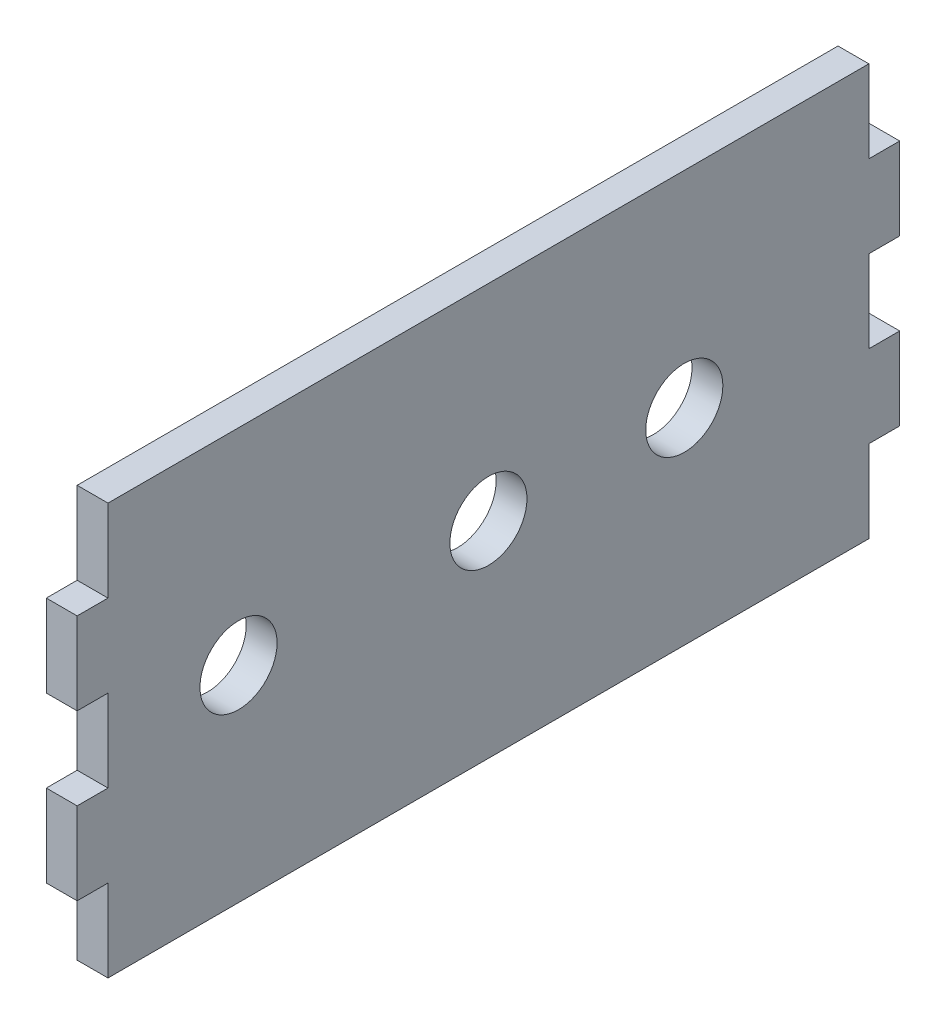
SolidWorks part; units mm, degrees
ref_plane "Alzado" through (0, 0, 0) normal (0, 0, 1) x (1, 0, 0)
ref_plane "Planta" through (0, 0, 0) normal (0, 1, 0) x (1, 0, 0)
ref_plane "Vista lateral" through (0, 0, 0) normal (1, 0, 0) x (0, 0, -1)
sketch "Croquis1" plane through (0, 0, 0) normal (1, 0, 0) x (0, 0, -1)
  line L0 (0, 40) -> (0, -40) construction
  line L1 (80, -40) -> (-80, -40)
  line L2 (80, -40) -> (80, 40)
  line L3 (80, 40) -> (-80, 40)
  line L4 (-80, -40) -> (-80, 40)
  line L5 (80, -40) -> (-80, 40) construction
  line L6 (80, 40) -> (-80, -40) construction
  point P0 (0, 0)
  dimension "D1" = 160
  dimension "D2" = 80
extrude "Saliente-Extruir1" add sketch "Croquis1" along normal blind 6
sketch "Croquis2" plane through (6, 0, 0) normal (1, 0, 0) x (0, 0, -1)
  line L1 (-80, -40) -> (80, -40) construction
  line L2 (-80, 40) -> (-80, -40) construction
  circle A0 centre (-48.61, 0) radius 7.5
  circle A1 centre (0, 0) radius 7.5
  circle A2 centre (38.1, 0) radius 7.5
  dimension "D1" = 15
  dimension "D2" = 80
  dimension "D3" = 40
  dimension "D4" = 40
  dimension "D5" = 40
  dimension "D6" = 48.61
  dimension "D7" = 38.1
extrude "Cortar-Extruir1" cut sketch "Croquis2" against normal blind 6
sketch "Croquis3" plane through (6, 0, 0) normal (1, 0, 0) x (0, 0, -1)
  line L0 (0, 40) -> (0, -40) construction
  line L1 (80, 40) -> (-80, 40) construction
  line L2 (-80, -40) -> (80, -40) construction
  line L4 (0, 0) -> (-80, 0) construction
  line L5 (-80, 40) -> (-74, 40)
  line L6 (-80, 40) -> (-80, 24)
  line L7 (-80, 24) -> (-74, 24)
  line L8 (-74, 40) -> (-74, 24)
  line L9 (-80, 40) -> (-80, -40) construction
  line L10 (-80, -24) -> (-74, -24)
  line L11 (-74, -40) -> (-74, -24)
  line L12 (-80, -40) -> (-74, -40)
  line L13 (-80, -40) -> (-80, -24)
  line L14 (80, -40) -> (80, -24)
  line L15 (80, -40) -> (74, -40)
  line L16 (74, -40) -> (74, -24)
  line L17 (80, -24) -> (74, -24)
  line L18 (80, 24) -> (74, 24)
  line L19 (74, 40) -> (74, 24)
  line L20 (80, 40) -> (74, 40)
  line L21 (80, 40) -> (80, 24)
  line L22 (80, -8) -> (74, -8)
  line L23 (-80, 8) -> (-74, 8)
  line L24 (-80, 8) -> (-80, -8)
  line L25 (-80, -8) -> (-74, -8)
  line L26 (-74, 8) -> (-74, -8)
  line L27 (74, 8) -> (74, -8)
  line L28 (80, 8) -> (74, 8)
  line L29 (80, 8) -> (80, -8)
  point P32 (-77, 8)
  point P33 (-77, -8)
  point P34 (-74, 0)
  dimension "D1" = 16
  dimension "D2" = 6
  dimension "D3" = 8
  dimension "D4" = 8
  dimension "D5" = 6
extrude "Cortar-Extruir2" cut sketch "Croquis3" against normal blind 6
